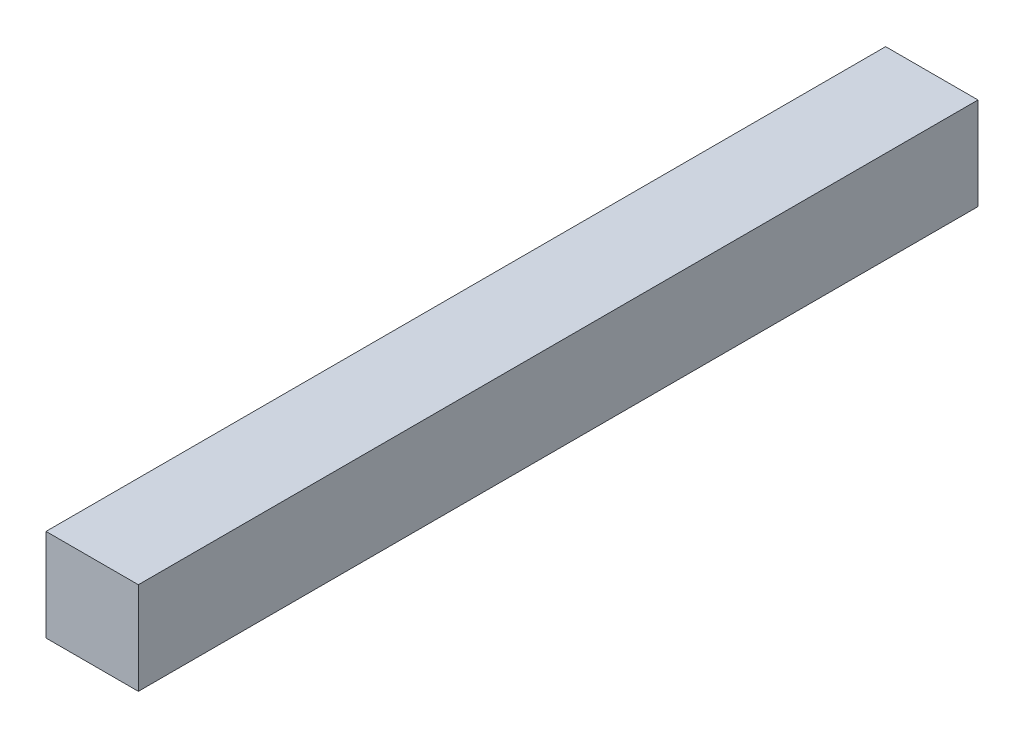
SolidWorks part; units mm, degrees
ref_plane "Face" through (0, 0, 0) normal (0, 0, 1) x (1, 0, 0)
ref_plane "Dessus" through (0, 0, 0) normal (0, 1, 0) x (1, 0, 0)
ref_plane "Droite" through (0, 0, 0) normal (1, 0, 0) x (0, 0, -1)
sketch "Esquisse1" plane through (0, 0, 0) normal (0, 0, 1) x (1, 0, 0)
  line L1 (0, 0) -> (22, 0)
  line L2 (0, 0) -> (0, 22)
  line L3 (0, 22) -> (22, 22)
  line L4 (22, 0) -> (22, 22)
  dimension "D1" = 22
  dimension "D2" = 22
extrude "Extrusion1" add sketch "Esquisse1" against normal blind 200
